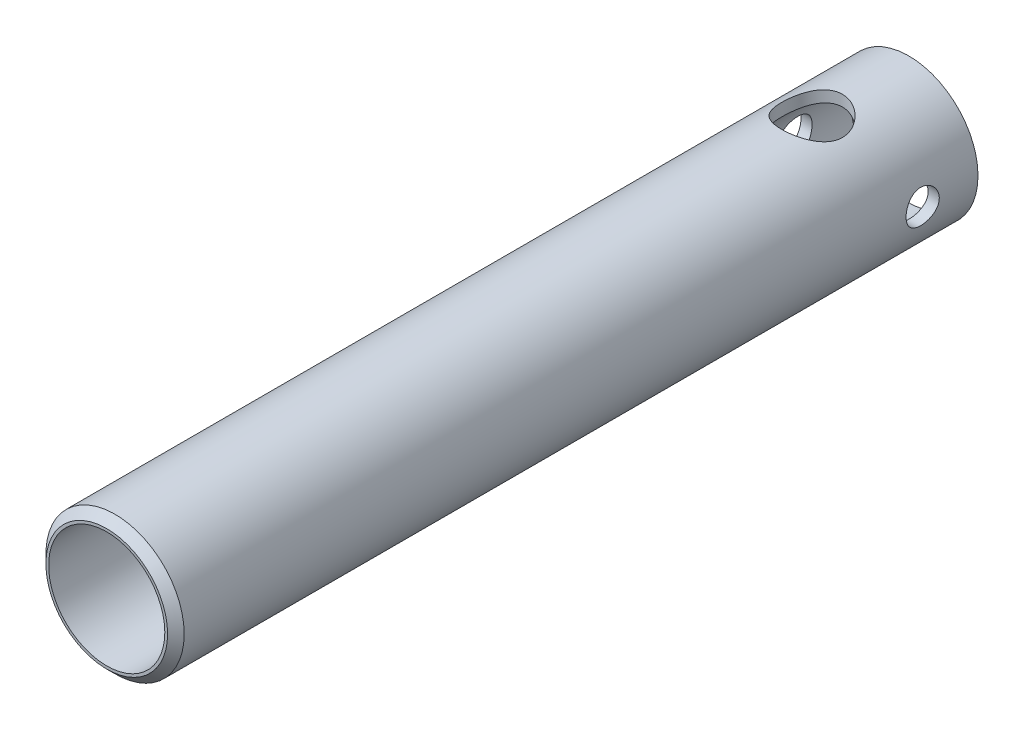
SolidWorks part; units mm, degrees
material "AISI 1020"
ref_plane "Front Plane" through (0, 0, 0) normal (0, 0, 1) x (1, 0, 0)
ref_plane "Top Plane" through (0, 0, 0) normal (0, 1, 0) x (1, 0, 0)
ref_plane "Right Plane" through (0, 0, 0) normal (1, 0, 0) x (0, 0, -1)
sketch "Sketch1" plane through (0, 0, 0) normal (0, 0, 1) x (1, 0, 0)
  circle A0 centre (0, 0) radius 25
  circle A1 centre (0, 0) radius 21
  dimension "D1" = 50
  dimension "D2" = 42
extrude "Boss-Extrude1" add sketch "Sketch1" along normal mid plane 290
chamfer "Chamfer1" distance 3 angle 45 1 edges at (25, 0, 145)
sketch "Sketch2" plane through (0, 0, 0) normal (0, 1, 0) x (1, 0, 0)
  line L0 (21, 145) -> (-21, 145) construction
  circle A0 centre (0, 110) radius 11
  point P4 (0, 0)
  dimension "D1" = 22
  dimension "D2" = 35
extrude "Cut-Extrude1" cut sketch "Sketch2" against normal through all both and the other way through all
sketch "Sketch3" plane through (0, 0, 0) normal (1, 0, 0) x (0, 0, -1)
  line L0 (145, -25) -> (145, 25) construction
  circle A0 centre (125, 0) radius 6
  point P4 (0, 0)
  dimension "D1" = 12
  dimension "D2" = 20
extrude "Cut-Extrude2" cut sketch "Sketch3" against normal through all both and the other way through all
sketch "Sketch4" plane through (0, 0, 0) normal (0, 1, 0) x (1, 0, 0)
  line L0 (-22, -145) -> (22, -145) construction
  line L1 (-3, -95) -> (3, -95)
  line L2 (-3, -95) -> (-3, -20)
  line L3 (-3, -20) -> (3, -20)
  line L4 (3, -95) -> (3, -20)
  line L5 (-3, -95) -> (3, -20) construction
  line L6 (-3, -20) -> (3, -95) construction
  point P0 (0, -57.5)
  point P5 (0, 0)
  dimension "D1" = 75
  dimension "D2" = 6
  dimension "D3" = 50
extrude "Cut-Extrude3" cut sketch "Sketch4" against normal up to next
